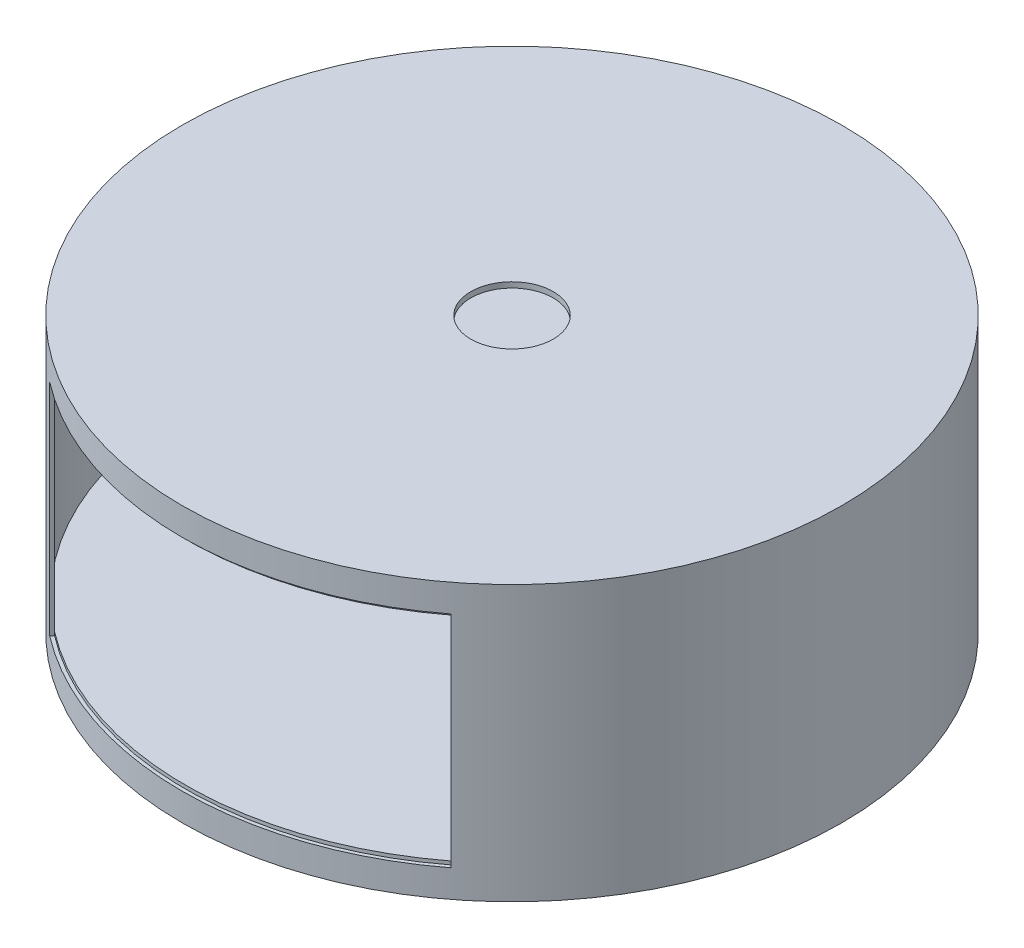
SolidWorks part; units mm, degrees
ref_plane "Front Plane" through (0, 0, 0) normal (0, 0, 1) x (1, 0, 0)
ref_plane "Top Plane" through (0, 0, 0) normal (0, 1, 0) x (1, 0, 0)
ref_plane "Right Plane" through (0, 0, 0) normal (1, 0, 0) x (0, 0, -1)
sketch "Sketch1" plane through (0, 0, 0) normal (0, 1, 0) x (1, 0, 0)
  circle A0 centre (0, 0) radius 152.4
  dimension "D1" = 304.8
extrude "Boss-Extrude1" add sketch "Sketch1" along normal mid plane 127 contours A0
sketch "Sketch2" plane through (0, 0, 0) normal (0, 1, 0) x (1, 0, 0)
  circle A0 centre (0, 0) radius 150.8125
  dimension "D1" = 301.625
extrude "Cut-Extrude1" cut sketch "Sketch2" against normal mid plane 98.425
sketch "Sketch3" plane through (0, 0, 0) normal (1, 0, 0) x (0, 0, -1)
  line L0 (-152.4, 50.8) -> (-152.4, -50.8)
  line L1 (-152.4, 63.5) -> (-152.4, -63.5) construction
  line L2 (-152.4, -50.8) -> (-150.8125, -50.8)
  line L3 (-150.8125, 49.2125) -> (-150.8125, -49.2125) construction
  line L4 (-150.8125, -50.8) -> (-150.8125, 50.8)
  line L5 (-150.8125, 50.8) -> (-152.4, 50.8)
  line L6 (152.4, 63.5) -> (-152.4, 63.5) construction
  line L7 (-152.4, -63.5) -> (152.4, -63.5) construction
  line L8 (0, 0) -> (0, 63.5) construction
  dimension "D1" = 12.7
  dimension "D2" = 12.7
revolve "Cut-Revolve1" cut sketch "Sketch3" angle 75 mid plane about L8
sketch "Sketch4" plane through (0, 63.5, 0) normal (0, 1, 0) x (1, 0, 0)
  circle A0 centre (0, 0) radius 19.05
  dimension "D1" = 38.1
extrude "Cut-Extrude2" cut sketch "Sketch4" against normal blind 2.54
equation "\"D2@Sketch3\"=\"D1@Sketch3\""
